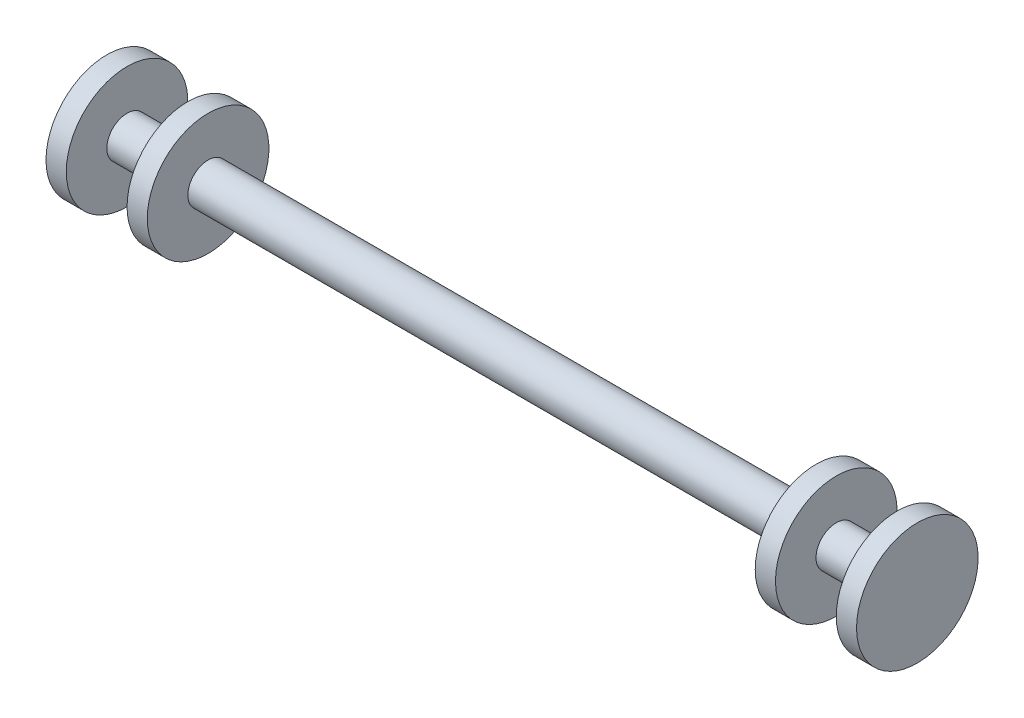
SolidWorks part; units mm, degrees
ref_plane "前视基准面" through (0, 0, 0) normal (0, 0, 1) x (1, 0, 0)
ref_plane "上视基准面" through (0, 0, 0) normal (0, 1, 0) x (1, 0, 0)
ref_plane "右视基准面" through (0, 0, 0) normal (1, 0, 0) x (0, 0, -1)
other "Configuration Table"
sketch "草图1" plane through (0, 0, 0) normal (0, 0, 1) x (1, 0, 0)
  line L0 (30, 0) -> (-30, 0)
  line L1 (-30, 0) -> (-30, 4)
  line L2 (-30, 4) -> (-32, 4)
  line L3 (-32, 4) -> (-32, 0)
  line L4 (-32, 0) -> (-38, 0)
  line L5 (-38, 0) -> (-38, 4)
  line L6 (-38, 4) -> (-40, 4)
  line L7 (-40, 4) -> (-40, 0)
  line L8 (30, 0) -> (30, 4)
  line L9 (30, 4) -> (32, 4)
  line L10 (32, 4) -> (32, 0)
  line L11 (32, 0) -> (38, 0)
  line L12 (38, 0) -> (38, 4)
  line L13 (38, 4) -> (40, 4)
  line L14 (40, 4) -> (40, 0)
  line L15 (-40, -2) -> (40, -2)
  line L16 (-40, -2) -> (-40, 0)
  line L17 (40, 0) -> (40, -2)
  point P4 (0, 0)
  point P8 (-30, 0)
  point P22 (40.448, -2)
  dimension "D1" = 60
  dimension "D2" = 2
  dimension "D3" = 2
  dimension "D4" = 6
  dimension "D5" = 2
  dimension "D6" = 2
  dimension "D7" = 6
  dimension "D8" = 4
  dimension "D9" = 4
  dimension "D10" = 4
  dimension "D11" = 4
  dimension "D12" = 4
  dimension "D13" = 4
  dimension "D14" = 4
  dimension "D15" = 2
  dimension "D16" = 80
revolve "旋转1" add sketch "草图1" angle 360 about L15
